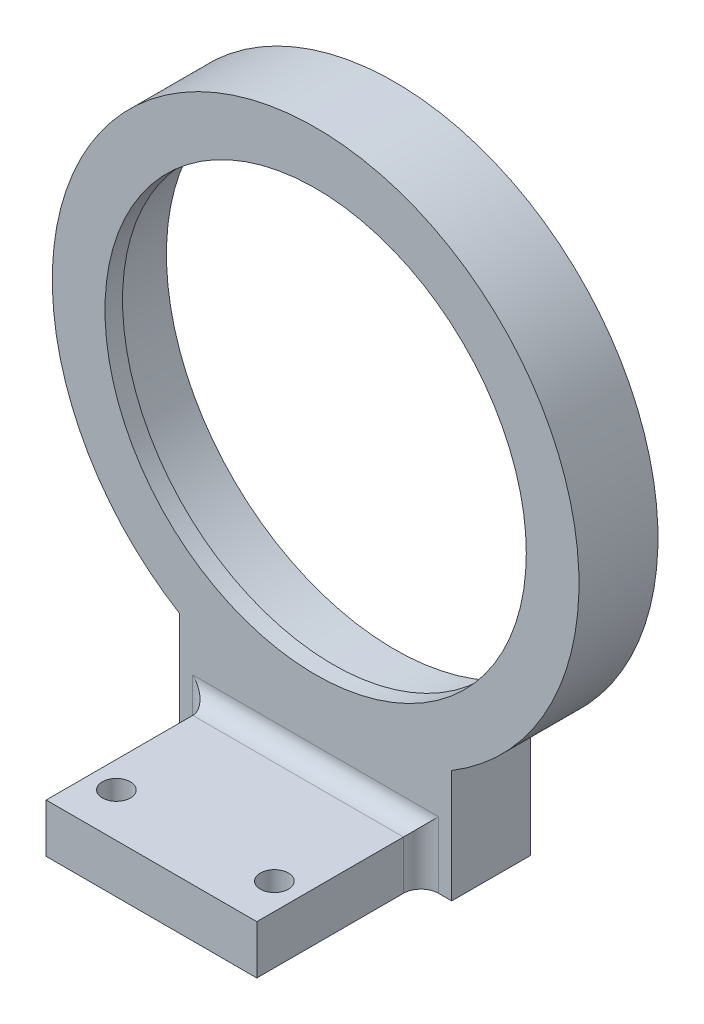
SolidWorks part; units mm, degrees
ref_plane "前视基准面" through (0, 0, 0) normal (0, 0, 1) x (1, 0, 0)
ref_plane "上视基准面" through (0, 0, 0) normal (0, 1, 0) x (1, 0, 0)
ref_plane "右视基准面" through (0, 0, 0) normal (1, 0, 0) x (0, 0, -1)
sketch "草图1" plane through (0, 0, 0) normal (0, 0, 1) x (1, 0, 0)
  line L1 (-15.5, -38) -> (15.5, -38)
  line L2 (-15.5, -38) -> (-15.5, -25.6856)
  line L4 (15.5, -38) -> (15.5, -25.6856)
  line L5 (0, -26) -> (0, -38) construction
  line L6 (-15.5, -31.8428) -> (15.5, -31.8428) construction
  circle A0 centre (0, 0) radius 26
  arc A1 (15.5, -25.6856) -> (-15.5, -25.6856) centre (0, 0) ccw
  point P4 (0, -31.8428)
  dimension "D1" = 52
  dimension "D2" = 60
  dimension "D3" = 31
  dimension "D4" = 38
extrude "凸台-拉伸1" add sketch "草图1" along normal blind 7
sketch "草图4" plane through (0, 0, 7) normal (0, 0, 1) x (1, 0, 0)
  circle A0 centre (0, 0) radius 30
  circle A1 centre (0, 0) radius 24
  dimension "D1" = 60
  dimension "D2" = 48
extrude "凸台-拉伸4" add sketch "草图4" along normal blind 2
sketch "草图5" plane through (0, 0, 7) normal (0, 0, 1) x (1, 0, 0)
  line L0 (0, 0) -> (0, -41.913) construction
  line L1 (-15.5, -38) -> (15.5, -38) construction
  line L2 (-12, -38) -> (12, -38)
  line L3 (-12, -38) -> (-12, -33)
  line L4 (-12, -33) -> (12, -33)
  line L5 (12, -38) -> (12, -33)
  dimension "D1" = 24
  dimension "D2" = 5
extrude "凸台-拉伸5" add sketch "草图5" along normal blind 20.7
sketch "草图6" plane through (0, 0, 7) normal (0, 0, 1) x (1, 0, 0)
  line L0 (-15.5, -25.6856) -> (-15.5, -38) construction
  line L1 (15.5, -38) -> (15.5, -25.6856) construction
  line L2 (12, -38) -> (15.5, -38) construction
  line L3 (12, -38) -> (12, -33) construction
  line L4 (12, -33) -> (-12, -33) construction
  line L5 (-12, -33) -> (-12, -38) construction
  line L6 (-15.5, -38) -> (-12, -38) construction
  line L7 (-15.5, -25.6856) -> (-15.5, -38)
  line L8 (15.5, -38) -> (15.5, -25.6856)
  line L9 (12, -38) -> (15.5, -38)
  line L10 (12, -38) -> (12, -33)
  line L11 (12, -33) -> (-12, -33)
  line L12 (-12, -33) -> (-12, -38)
  line L13 (-15.5, -38) -> (-12, -38)
  circle A0 centre (0, 0) radius 30 construction
  arc A1 (-15.5, -25.6856) -> (15.5, -25.6856) centre (0, 0) ccw
extrude "凸台-拉伸6" add sketch "草图6" along normal up to surface (2 mm away) up to face at (30, 0, 9)
sketch "草图9" plane through (0, -38, 0) normal (0, -1, 0) x (1, 0, 0)
  line L8 (15.5, 0) -> (15.5, 9)
  line L9 (15.5, 9) -> (12, 9)
  line L10 (12, 9) -> (12, 27.7)
  line L11 (12, 27.7) -> (-12, 27.7)
  line L12 (-12, 27.7) -> (-12, 9)
  line L13 (-12, 9) -> (-15.5, 9)
  line L14 (-15.5, 9) -> (-15.5, 0)
  line L15 (-15.5, 0) -> (15.5, 0)
  line L16 (15.5, 0) -> (15.5, 9)
  line L17 (15.5, 9) -> (12, 9)
  line L18 (12, 9) -> (12, 27.7)
  line L19 (12, 27.7) -> (-12, 27.7)
  line L20 (-12, 27.7) -> (-12, 9)
  line L21 (-12, 9) -> (-15.5, 9)
  line L22 (-15.5, 9) -> (-15.5, 0)
  line L23 (-15.5, 0) -> (15.5, 0)
  dimension "D1" = 0
extrude "凸台-拉伸7" add sketch "草图9" along normal blind 0.56
sketch "草图7" plane through (0, -33, 0) normal (0, 1, 0) x (1, 0, 0)
  line L0 (0, -27.7) -> (0, 6.0944) construction
  line L1 (12, -27.7) -> (-12, -27.7) construction
  circle A0 centre (9, -22.7) radius 1.6
  circle A1 centre (-9, -22.7) radius 1.6
  dimension "D1" = 18
  dimension "D2" = 5
  dimension "D3" = 3.2
extrude "切除-拉伸1" cut sketch "草图7" against normal blind 16
fillet "圆角1" radius 2 1 edges at (0, -33, 9)
fillet "圆角2" radius 2 2 edges at (12, -32.4142, 9.5858) (12, -34.78, 9)
fillet "圆角3" radius 2 2 edges at (-12, -32.4142, 9.5858) (-12, -34.78, 9)
